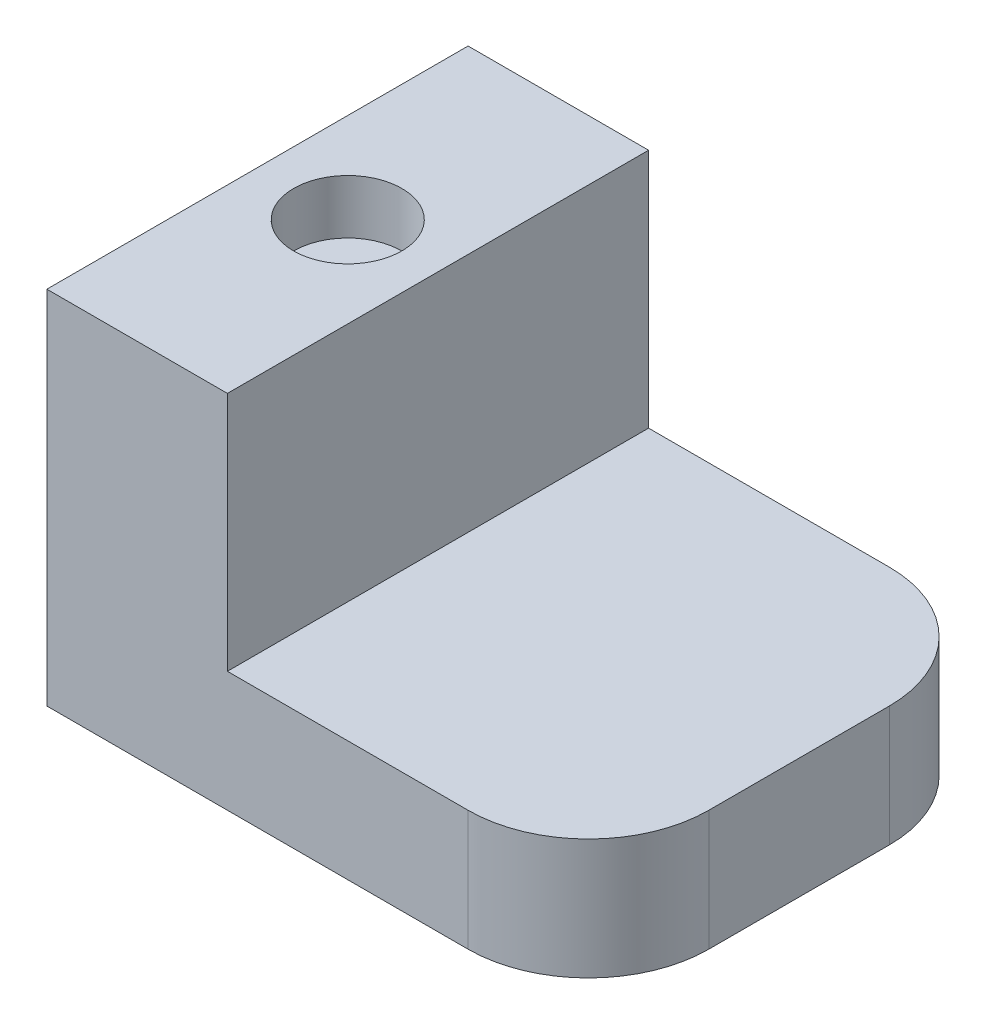
SolidWorks part; units mm, degrees
material "티타늄 Ti-8Mn, 강화"
ref_plane "정면" through (0, 0, 0) normal (0, 0, 1) x (1, 0, 0)
ref_plane "윗면" through (0, 0, 0) normal (0, 1, 0) x (1, 0, 0)
ref_plane "우측면" through (0, 0, 0) normal (1, 0, 0) x (0, 0, -1)
sketch "스케치4" plane through (0, 0, 0) normal (0, 0, 1) x (1, 0, 0)
  line L1 (0, 0) -> (90, 0)
  line L2 (0, 0) -> (0, 60)
  line L3 (0, 60) -> (90, 60)
  line L4 (90, 0) -> (90, 60)
  dimension "D1" = 90
  dimension "D2" = 60
extrude "보스-돌출1" add sketch "스케치4" along normal blind 70
sketch "스케치5" plane through (0, 0, 70) normal (0, 0, 1) x (1, 0, 0)
  line L1 (90, 60) -> (30, 60)
  line L2 (90, 60) -> (90, 20)
  line L3 (90, 20) -> (30, 20)
  line L4 (30, 60) -> (30, 20)
  dimension "D1" = 30
  dimension "D2" = 20
extrude "컷-돌출1" cut sketch "스케치5" against normal blind 70
sketch "스케치6" plane through (0, 60, 0) normal (0, 1, 0) x (1, 0, 0)
  line L0 (15, 0) -> (15, -70) construction
  line L1 (30, 0) -> (0, 0) construction
  line L2 (30, -70) -> (0, -70) construction
  circle A0 centre (15, -35) radius 9
  dimension "D1" = 18
extrude "컷-돌출2" cut sketch "스케치6" against normal blind 9
fillet "필렛1" radius 20 2 edges at (90, 10, 0) (90, 10, 70)
